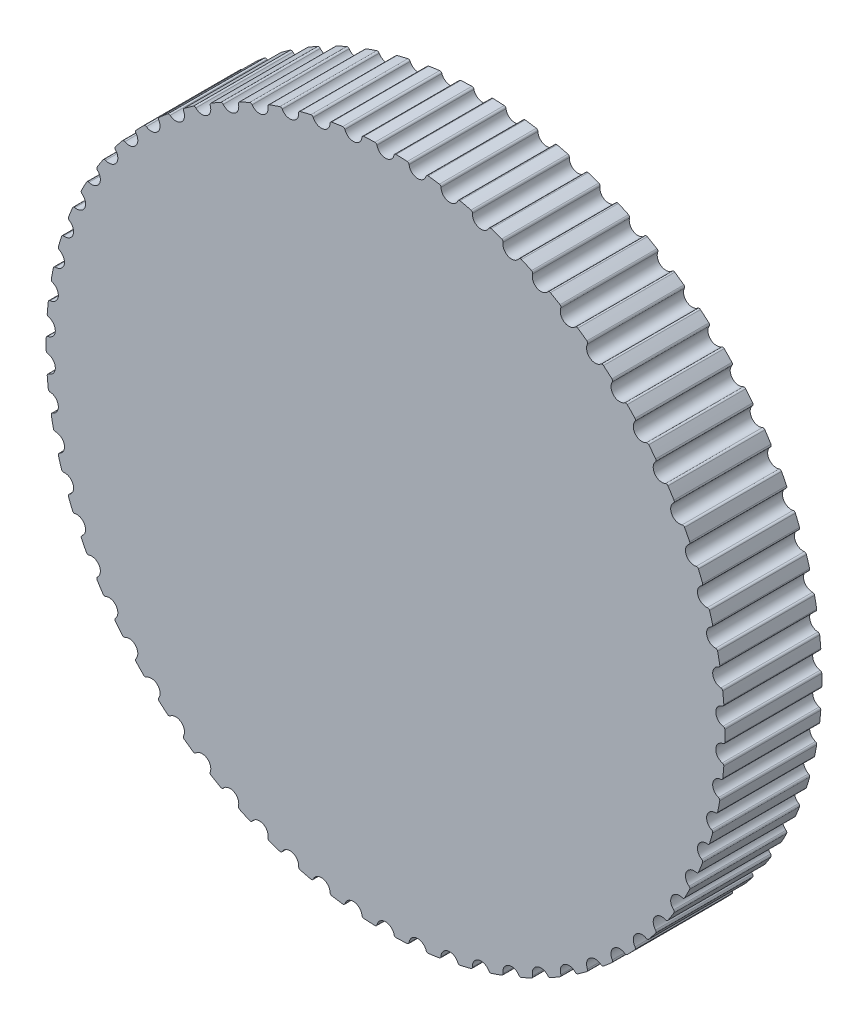
SolidWorks part; units mm, degrees
ref_plane "Front Plane" through (0, 0, 0) normal (0, 0, 1) x (1, 0, 0)
ref_plane "Top Plane" through (0, 0, 0) normal (0, 1, 0) x (1, 0, 0)
ref_plane "Right Plane" through (0, 0, 0) normal (1, 0, 0) x (0, 0, -1)
sketch "Sketch1" plane through (0, 0, 0) normal (0, 0, 1) x (1, 0, 0)
  arc A0 (-0.655, 20.9898) -> (0.655, 20.9898) centre (0, 0) ccw
  arc A1 (-0.5287, 20.8902) -> (0.5287, 20.8902) centre (0, 21) ccw
  arc A2 (0.5287, 20.8902) -> (0.655, 20.9898) centre (0.6511, 20.8648) cw
  arc A3 (-0.5287, 20.8902) -> (-0.655, 20.9898) centre (-0.6511, 20.8648) ccw
  arc A4 (1.3432, 20.957) -> (2.6473, 20.8325) centre (0, 0) ccw
  arc A5 (1.4594, 20.8459) -> (1.3432, 20.957) centre (1.3352, 20.8323) ccw
  arc A6 (1.4594, 20.8459) -> (2.5121, 20.7454) centre (1.9962, 20.9049) ccw
  arc A7 (2.5121, 20.7454) -> (2.6473, 20.8325) centre (2.6315, 20.7085) cw
  arc A8 (3.3292, 20.7344) -> (4.6155, 20.4865) centre (0, 0) ccw
  arc A9 (3.4343, 20.6128) -> (3.3292, 20.7344) centre (3.3093, 20.611) ccw
  arc A10 (3.4343, 20.6128) -> (4.4727, 20.4127) centre (3.9743, 20.6205) ccw
  arc A11 (4.4727, 20.4127) -> (4.6155, 20.4865) centre (4.5881, 20.3646) cw
  arc A12 (5.285, 20.3241) -> (6.542, 19.955) centre (0, 0) ccw
  arc A13 (5.3782, 20.193) -> (5.285, 20.3241) centre (5.2536, 20.2031) ccw
  arc A14 (5.3782, 20.193) -> (6.3928, 19.8951) centre (5.9164, 20.1494) ccw
  arc A15 (6.3928, 19.8951) -> (6.542, 19.955) centre (6.5031, 19.8362) cw
  arc A16 (7.193, 19.7297) -> (8.4092, 19.2428) centre (0, 0) ccw
  arc A17 (7.2733, 19.5903) -> (7.193, 19.7297) centre (7.1502, 19.6122) ccw
  arc A18 (7.2733, 19.5903) -> (8.255, 19.1973) centre (7.8049, 19.4957) ccw
  arc A19 (8.255, 19.1973) -> (8.4092, 19.2428) centre (8.3592, 19.1283) cw
  arc A20 (9.0359, 18.9566) -> (10.2003, 18.3563) centre (0, 0) ccw
  arc A21 (9.1025, 18.8103) -> (9.0359, 18.9566) centre (8.9821, 18.8438) ccw
  arc A22 (9.1025, 18.8103) -> (10.0424, 18.3257) centre (9.6228, 18.6655) ccw
  arc A23 (10.0424, 18.3257) -> (10.2003, 18.3563) centre (10.1396, 18.2471) cw
  arc A24 (10.7969, 18.0119) -> (11.899, 17.3036) centre (0, 0) ccw
  arc A25 (10.8493, 17.8598) -> (10.7969, 18.0119) centre (10.7326, 17.9046) ccw
  arc A26 (10.8493, 17.8598) -> (11.7389, 17.2881) centre (11.3535, 17.6663) ccw
  arc A27 (11.7389, 17.2881) -> (11.899, 17.3036) centre (11.8281, 17.2006) cw
  arc A28 (12.4601, 16.904) -> (13.4899, 16.0942) centre (0, 0) ccw
  arc A29 (12.4979, 16.7477) -> (12.4601, 16.904) centre (12.386, 16.8034) ccw
  arc A30 (12.4979, 16.7477) -> (13.3291, 16.094) centre (12.9813, 16.5071) ccw
  arc A31 (13.3291, 16.094) -> (13.4899, 16.0942) centre (13.4096, 15.9984) cw
  arc A32 (14.0105, 15.643) -> (14.9587, 14.739) centre (0, 0) ccw
  arc A33 (14.0333, 15.4838) -> (14.0105, 15.643) centre (13.9272, 15.5499) ccw
  arc A34 (14.0333, 15.4838) -> (14.7986, 14.7541) centre (14.4917, 15.1984) ccw
  arc A35 (14.7986, 14.7541) -> (14.9587, 14.739) centre (14.8696, 14.6513) cw
  arc A36 (15.4341, 14.2404) -> (16.292, 13.2504) centre (0, 0) ccw
  arc A37 (15.4416, 14.0798) -> (15.4341, 14.2404) centre (15.3422, 14.1557) ccw
  arc A38 (15.4416, 14.0798) -> (16.134, 13.2806) centre (15.8707, 13.7521) ccw
  arc A39 (16.134, 13.2806) -> (16.292, 13.2504) centre (16.195, 13.1715) cw
  arc A40 (16.7178, 12.7088) -> (17.4777, 11.6417) centre (0, 0) ccw
  arc A41 (16.71, 12.5482) -> (16.7178, 12.7088) centre (16.6183, 12.6332) ccw
  arc A42 (16.71, 12.5482) -> (17.3234, 11.6868) centre (17.1061, 12.1812) ccw
  arc A43 (17.3234, 11.6868) -> (17.4777, 11.6417) centre (17.3737, 11.5724) cw
  arc A44 (17.8502, 11.0622) -> (18.5052, 9.9276) centre (0, 0) ccw
  arc A45 (17.8271, 10.903) -> (17.8502, 11.0622) centre (17.7439, 10.9963) ccw
  arc A46 (17.8271, 10.903) -> (18.3559, 9.9872) centre (18.1865, 10.5) ccw
  arc A47 (18.3559, 9.9872) -> (18.5052, 9.9276) centre (18.395, 9.8685) cw
  arc A48 (18.8209, 9.3153) -> (19.3651, 8.1236) centre (0, 0) ccw
  arc A49 (18.7828, 9.1591) -> (18.8209, 9.3153) centre (18.7088, 9.2598) ccw
  arc A50 (18.7828, 9.1591) -> (19.2221, 8.1972) centre (19.1023, 8.7237) ccw
  arc A51 (19.2221, 8.1972) -> (19.3651, 8.1236) centre (19.2498, 8.0753) cw
  arc A52 (19.6211, 7.4841) -> (20.0496, 6.2461) centre (0, 0) ccw
  arc A53 (19.5684, 7.3322) -> (19.6211, 7.4841) centre (19.5043, 7.4395) ccw
  arc A54 (19.5684, 7.3322) -> (19.9142, 6.3329) centre (19.845, 6.8684) ccw
  arc A55 (19.9142, 6.3329) -> (20.0496, 6.2461) centre (19.9303, 6.2089) cw
  arc A56 (20.2437, 5.5851) -> (20.5525, 4.312) centre (0, 0) ccw
  arc A57 (20.1767, 5.4389) -> (20.2437, 5.5851) centre (20.1232, 5.5518) ccw
  arc A58 (20.1767, 5.4389) -> (20.426, 4.4112) centre (20.408, 4.9509) ccw
  arc A59 (20.426, 4.4112) -> (20.5525, 4.312) centre (20.4302, 4.2863) cw
  arc A60 (20.6829, 3.6355) -> (20.8694, 2.3388) centre (0, 0) ccw
  arc A61 (20.6024, 3.4963) -> (20.6829, 3.6355) centre (20.5598, 3.6139) ccw
  arc A62 (20.6024, 3.4963) -> (20.7529, 2.4496) centre (20.7863, 2.9886) ccw
  arc A63 (20.7529, 2.4496) -> (20.8694, 2.3388) centre (20.7451, 2.3249) cw
  arc A64 (20.9348, 1.653) -> (20.9972, 0.3445) centre (0, 0) ccw
  arc A65 (20.8414, 1.5221) -> (20.9348, 1.653) centre (20.8102, 1.6432) ccw
  arc A66 (20.8414, 1.5221) -> (20.8917, 0.4659) centre (20.9762, 0.9992) ccw
  arc A67 (20.8917, 0.4659) -> (20.9972, 0.3445) centre (20.8722, 0.3424) cw
  arc A68 (20.9972, -0.3445) -> (20.9348, -1.653) centre (0, 0) ccw
  arc A69 (20.8917, -0.4659) -> (20.9972, -0.3445) centre (20.8722, -0.3424) ccw
  arc A70 (20.8917, -0.4659) -> (20.8414, -1.5221) centre (20.9762, -0.9992) ccw
  arc A71 (20.8414, -1.5221) -> (20.9348, -1.653) centre (20.8102, -1.6432) cw
  arc A72 (20.8694, -2.3388) -> (20.6829, -3.6355) centre (0, 0) ccw
  arc A73 (20.7529, -2.4496) -> (20.8694, -2.3388) centre (20.7451, -2.3249) ccw
  arc A74 (20.7529, -2.4496) -> (20.6024, -3.4963) centre (20.7863, -2.9886) ccw
  arc A75 (20.6024, -3.4963) -> (20.6829, -3.6355) centre (20.5598, -3.6139) cw
  arc A76 (20.5525, -4.312) -> (20.2437, -5.5851) centre (0, 0) ccw
  arc A77 (20.426, -4.4112) -> (20.5525, -4.312) centre (20.4302, -4.2863) ccw
  arc A78 (20.426, -4.4112) -> (20.1767, -5.4389) centre (20.408, -4.9509) ccw
  arc A79 (20.1767, -5.4389) -> (20.2437, -5.5851) centre (20.1232, -5.5518) cw
  arc A80 (20.0496, -6.2461) -> (19.6211, -7.4841) centre (0, 0) ccw
  arc A81 (19.9142, -6.3329) -> (20.0496, -6.2461) centre (19.9303, -6.2089) ccw
  arc A82 (19.9142, -6.3329) -> (19.5684, -7.3322) centre (19.845, -6.8684) ccw
  arc A83 (19.5684, -7.3322) -> (19.6211, -7.4841) centre (19.5043, -7.4395) cw
  arc A84 (19.3651, -8.1236) -> (18.8209, -9.3153) centre (0, 0) ccw
  arc A85 (19.2221, -8.1972) -> (19.3651, -8.1236) centre (19.2498, -8.0753) ccw
  arc A86 (19.2221, -8.1972) -> (18.7828, -9.1591) centre (19.1023, -8.7237) ccw
  arc A87 (18.7828, -9.1591) -> (18.8209, -9.3153) centre (18.7088, -9.2598) cw
  arc A88 (18.5052, -9.9276) -> (17.8502, -11.0622) centre (0, 0) ccw
  arc A89 (18.3559, -9.9872) -> (18.5052, -9.9276) centre (18.395, -9.8685) ccw
  arc A90 (18.3559, -9.9872) -> (17.8271, -10.903) centre (18.1865, -10.5) ccw
  arc A91 (17.8271, -10.903) -> (17.8502, -11.0622) centre (17.7439, -10.9963) cw
  arc A92 (17.4777, -11.6417) -> (16.7178, -12.7088) centre (0, 0) ccw
  arc A93 (17.3234, -11.6868) -> (17.4777, -11.6417) centre (17.3737, -11.5724) ccw
  arc A94 (17.3234, -11.6868) -> (16.71, -12.5482) centre (17.1061, -12.1812) ccw
  arc A95 (16.71, -12.5482) -> (16.7178, -12.7088) centre (16.6183, -12.6332) cw
  arc A96 (16.292, -13.2504) -> (15.4341, -14.2404) centre (0, 0) ccw
  arc A97 (16.134, -13.2806) -> (16.292, -13.2504) centre (16.195, -13.1715) ccw
  arc A98 (16.134, -13.2806) -> (15.4416, -14.0798) centre (15.8707, -13.7521) ccw
  arc A99 (15.4416, -14.0798) -> (15.4341, -14.2404) centre (15.3422, -14.1557) cw
  arc A100 (14.9587, -14.739) -> (14.0105, -15.643) centre (0, 0) ccw
  arc A101 (14.7986, -14.7541) -> (14.9587, -14.739) centre (14.8696, -14.6513) ccw
  arc A102 (14.7986, -14.7541) -> (14.0333, -15.4838) centre (14.4917, -15.1984) ccw
  arc A103 (14.0333, -15.4838) -> (14.0105, -15.643) centre (13.9272, -15.5499) cw
  arc A104 (13.4899, -16.0942) -> (12.4601, -16.904) centre (0, 0) ccw
  arc A105 (13.3291, -16.094) -> (13.4899, -16.0942) centre (13.4096, -15.9984) ccw
  arc A106 (13.3291, -16.094) -> (12.4979, -16.7477) centre (12.9813, -16.5071) ccw
  arc A107 (12.4979, -16.7477) -> (12.4601, -16.904) centre (12.386, -16.8034) cw
  arc A108 (11.899, -17.3036) -> (10.7969, -18.0119) centre (0, 0) ccw
  arc A109 (11.7389, -17.2881) -> (11.899, -17.3036) centre (11.8281, -17.2006) ccw
  arc A110 (11.7389, -17.2881) -> (10.8493, -17.8598) centre (11.3535, -17.6663) ccw
  arc A111 (10.8493, -17.8598) -> (10.7969, -18.0119) centre (10.7326, -17.9046) cw
  arc A112 (10.2003, -18.3563) -> (9.0359, -18.9566) centre (0, 0) ccw
  arc A113 (10.0424, -18.3257) -> (10.2003, -18.3563) centre (10.1396, -18.2471) ccw
  arc A114 (10.0424, -18.3257) -> (9.1025, -18.8103) centre (9.6228, -18.6655) ccw
  arc A115 (9.1025, -18.8103) -> (9.0359, -18.9566) centre (8.9821, -18.8438) cw
  arc A116 (8.4092, -19.2428) -> (7.193, -19.7297) centre (0, 0) ccw
  arc A117 (8.255, -19.1973) -> (8.4092, -19.2428) centre (8.3592, -19.1283) ccw
  arc A118 (8.255, -19.1973) -> (7.2733, -19.5903) centre (7.8049, -19.4957) ccw
  arc A119 (7.2733, -19.5903) -> (7.193, -19.7297) centre (7.1502, -19.6122) cw
  arc A120 (6.542, -19.955) -> (5.285, -20.3241) centre (0, 0) ccw
  arc A121 (6.3928, -19.8951) -> (6.542, -19.955) centre (6.5031, -19.8362) ccw
  arc A122 (6.3928, -19.8951) -> (5.3782, -20.193) centre (5.9164, -20.1494) ccw
  arc A123 (5.3782, -20.193) -> (5.285, -20.3241) centre (5.2536, -20.2031) cw
  arc A124 (4.6155, -20.4865) -> (3.3292, -20.7344) centre (0, 0) ccw
  arc A125 (4.4727, -20.4127) -> (4.6155, -20.4865) centre (4.5881, -20.3646) ccw
  arc A126 (4.4727, -20.4127) -> (3.4343, -20.6128) centre (3.9743, -20.6205) ccw
  arc A127 (3.4343, -20.6128) -> (3.3292, -20.7344) centre (3.3093, -20.611) cw
  arc A128 (2.6473, -20.8325) -> (1.3432, -20.957) centre (0, 0) ccw
  arc A129 (2.5121, -20.7454) -> (2.6473, -20.8325) centre (2.6315, -20.7085) ccw
  arc A130 (2.5121, -20.7454) -> (1.4594, -20.8459) centre (1.9962, -20.9049) ccw
  arc A131 (1.4594, -20.8459) -> (1.3432, -20.957) centre (1.3352, -20.8323) cw
  arc A132 (0.655, -20.9898) -> (-0.655, -20.9898) centre (0, 0) ccw
  arc A133 (0.5287, -20.8902) -> (0.655, -20.9898) centre (0.6511, -20.8648) ccw
  arc A134 (0.5287, -20.8902) -> (-0.5287, -20.8902) centre (0, -21) ccw
  arc A135 (-0.5287, -20.8902) -> (-0.655, -20.9898) centre (-0.6511, -20.8648) cw
  arc A136 (-1.3432, -20.957) -> (-2.6473, -20.8325) centre (0, 0) ccw
  arc A137 (-1.4594, -20.8459) -> (-1.3432, -20.957) centre (-1.3352, -20.8323) ccw
  arc A138 (-1.4594, -20.8459) -> (-2.5121, -20.7454) centre (-1.9962, -20.9049) ccw
  arc A139 (-2.5121, -20.7454) -> (-2.6473, -20.8325) centre (-2.6315, -20.7085) cw
  arc A140 (-3.3292, -20.7344) -> (-4.6155, -20.4865) centre (0, 0) ccw
  arc A141 (-3.4343, -20.6128) -> (-3.3292, -20.7344) centre (-3.3093, -20.611) ccw
  arc A142 (-3.4343, -20.6128) -> (-4.4727, -20.4127) centre (-3.9743, -20.6205) ccw
  arc A143 (-4.4727, -20.4127) -> (-4.6155, -20.4865) centre (-4.5881, -20.3646) cw
  arc A144 (-5.285, -20.3241) -> (-6.542, -19.955) centre (0, 0) ccw
  arc A145 (-5.3782, -20.193) -> (-5.285, -20.3241) centre (-5.2536, -20.2031) ccw
  arc A146 (-5.3782, -20.193) -> (-6.3928, -19.8951) centre (-5.9164, -20.1494) ccw
  arc A147 (-6.3928, -19.8951) -> (-6.542, -19.955) centre (-6.5031, -19.8362) cw
  arc A148 (-7.193, -19.7297) -> (-8.4092, -19.2428) centre (0, 0) ccw
  arc A149 (-7.2733, -19.5903) -> (-7.193, -19.7297) centre (-7.1502, -19.6122) ccw
  arc A150 (-7.2733, -19.5903) -> (-8.255, -19.1973) centre (-7.8049, -19.4957) ccw
  arc A151 (-8.255, -19.1973) -> (-8.4092, -19.2428) centre (-8.3592, -19.1283) cw
  arc A152 (-9.0359, -18.9566) -> (-10.2003, -18.3563) centre (0, 0) ccw
  arc A153 (-9.1025, -18.8103) -> (-9.0359, -18.9566) centre (-8.9821, -18.8438) ccw
  arc A154 (-9.1025, -18.8103) -> (-10.0424, -18.3257) centre (-9.6228, -18.6655) ccw
  arc A155 (-10.0424, -18.3257) -> (-10.2003, -18.3563) centre (-10.1396, -18.2471) cw
  arc A156 (-10.7969, -18.0119) -> (-11.899, -17.3036) centre (0, 0) ccw
  arc A157 (-10.8493, -17.8598) -> (-10.7969, -18.0119) centre (-10.7326, -17.9046) ccw
  arc A158 (-10.8493, -17.8598) -> (-11.7389, -17.2881) centre (-11.3535, -17.6663) ccw
  arc A159 (-11.7389, -17.2881) -> (-11.899, -17.3036) centre (-11.8281, -17.2006) cw
  arc A160 (-12.4601, -16.904) -> (-13.4899, -16.0942) centre (0, 0) ccw
  arc A161 (-12.4979, -16.7477) -> (-12.4601, -16.904) centre (-12.386, -16.8034) ccw
  arc A162 (-12.4979, -16.7477) -> (-13.3291, -16.094) centre (-12.9813, -16.5071) ccw
  arc A163 (-13.3291, -16.094) -> (-13.4899, -16.0942) centre (-13.4096, -15.9984) cw
  arc A164 (-14.0105, -15.643) -> (-14.9587, -14.739) centre (0, 0) ccw
  arc A165 (-14.0333, -15.4838) -> (-14.0105, -15.643) centre (-13.9272, -15.5499) ccw
  arc A166 (-14.0333, -15.4838) -> (-14.7986, -14.7541) centre (-14.4917, -15.1984) ccw
  arc A167 (-14.7986, -14.7541) -> (-14.9587, -14.739) centre (-14.8696, -14.6513) cw
  arc A168 (-15.4341, -14.2404) -> (-16.292, -13.2504) centre (0, 0) ccw
  arc A169 (-15.4416, -14.0798) -> (-15.4341, -14.2404) centre (-15.3422, -14.1557) ccw
  arc A170 (-15.4416, -14.0798) -> (-16.134, -13.2806) centre (-15.8707, -13.7521) ccw
  arc A171 (-16.134, -13.2806) -> (-16.292, -13.2504) centre (-16.195, -13.1715) cw
  arc A172 (-16.7178, -12.7088) -> (-17.4777, -11.6417) centre (0, 0) ccw
  arc A173 (-16.71, -12.5482) -> (-16.7178, -12.7088) centre (-16.6183, -12.6332) ccw
  arc A174 (-16.71, -12.5482) -> (-17.3234, -11.6868) centre (-17.1061, -12.1812) ccw
  arc A175 (-17.3234, -11.6868) -> (-17.4777, -11.6417) centre (-17.3737, -11.5724) cw
  arc A176 (-17.8502, -11.0622) -> (-18.5052, -9.9276) centre (0, 0) ccw
  arc A177 (-17.8271, -10.903) -> (-17.8502, -11.0622) centre (-17.7439, -10.9963) ccw
  arc A178 (-17.8271, -10.903) -> (-18.3559, -9.9872) centre (-18.1865, -10.5) ccw
  arc A179 (-18.3559, -9.9872) -> (-18.5052, -9.9276) centre (-18.395, -9.8685) cw
  arc A180 (-18.8209, -9.3153) -> (-19.3651, -8.1236) centre (0, 0) ccw
  arc A181 (-18.7828, -9.1591) -> (-18.8209, -9.3153) centre (-18.7088, -9.2598) ccw
  arc A182 (-18.7828, -9.1591) -> (-19.2221, -8.1972) centre (-19.1023, -8.7237) ccw
  arc A183 (-19.2221, -8.1972) -> (-19.3651, -8.1236) centre (-19.2498, -8.0753) cw
  arc A184 (-19.6211, -7.4841) -> (-20.0496, -6.2461) centre (0, 0) ccw
  arc A185 (-19.5684, -7.3322) -> (-19.6211, -7.4841) centre (-19.5043, -7.4395) ccw
  arc A186 (-19.5684, -7.3322) -> (-19.9142, -6.3329) centre (-19.845, -6.8684) ccw
  arc A187 (-19.9142, -6.3329) -> (-20.0496, -6.2461) centre (-19.9303, -6.2089) cw
  arc A188 (-20.2437, -5.5851) -> (-20.5525, -4.312) centre (0, 0) ccw
  arc A189 (-20.1767, -5.4389) -> (-20.2437, -5.5851) centre (-20.1232, -5.5518) ccw
  arc A190 (-20.1767, -5.4389) -> (-20.426, -4.4112) centre (-20.408, -4.9509) ccw
  arc A191 (-20.426, -4.4112) -> (-20.5525, -4.312) centre (-20.4302, -4.2863) cw
  arc A192 (-20.6829, -3.6355) -> (-20.8694, -2.3388) centre (0, 0) ccw
  arc A193 (-20.6024, -3.4963) -> (-20.6829, -3.6355) centre (-20.5598, -3.6139) ccw
  arc A194 (-20.6024, -3.4963) -> (-20.7529, -2.4496) centre (-20.7863, -2.9886) ccw
  arc A195 (-20.7529, -2.4496) -> (-20.8694, -2.3388) centre (-20.7451, -2.3249) cw
  arc A196 (-20.9348, -1.653) -> (-20.9972, -0.3445) centre (0, 0) ccw
  arc A197 (-20.8414, -1.5221) -> (-20.9348, -1.653) centre (-20.8102, -1.6432) ccw
  arc A198 (-20.8414, -1.5221) -> (-20.8917, -0.4659) centre (-20.9762, -0.9992) ccw
  arc A199 (-20.8917, -0.4659) -> (-20.9972, -0.3445) centre (-20.8722, -0.3424) cw
  arc A200 (-20.9972, 0.3445) -> (-20.9348, 1.653) centre (0, 0) ccw
  arc A201 (-20.8917, 0.4659) -> (-20.9972, 0.3445) centre (-20.8722, 0.3424) ccw
  arc A202 (-20.8917, 0.4659) -> (-20.8414, 1.5221) centre (-20.9762, 0.9992) ccw
  arc A203 (-20.8414, 1.5221) -> (-20.9348, 1.653) centre (-20.8102, 1.6432) cw
  arc A204 (-20.8694, 2.3388) -> (-20.6829, 3.6355) centre (0, 0) ccw
  arc A205 (-20.7529, 2.4496) -> (-20.8694, 2.3388) centre (-20.7451, 2.3249) ccw
  arc A206 (-20.7529, 2.4496) -> (-20.6024, 3.4963) centre (-20.7863, 2.9886) ccw
  arc A207 (-20.6024, 3.4963) -> (-20.6829, 3.6355) centre (-20.5598, 3.6139) cw
  arc A208 (-20.5525, 4.312) -> (-20.2437, 5.5851) centre (0, 0) ccw
  arc A209 (-20.426, 4.4112) -> (-20.5525, 4.312) centre (-20.4302, 4.2863) ccw
  arc A210 (-20.426, 4.4112) -> (-20.1767, 5.4389) centre (-20.408, 4.9509) ccw
  arc A211 (-20.1767, 5.4389) -> (-20.2437, 5.5851) centre (-20.1232, 5.5518) cw
  arc A212 (-20.0496, 6.2461) -> (-19.6211, 7.4841) centre (0, 0) ccw
  arc A213 (-19.9142, 6.3329) -> (-20.0496, 6.2461) centre (-19.9303, 6.2089) ccw
  arc A214 (-19.9142, 6.3329) -> (-19.5684, 7.3322) centre (-19.845, 6.8684) ccw
  arc A215 (-19.5684, 7.3322) -> (-19.6211, 7.4841) centre (-19.5043, 7.4395) cw
  arc A216 (-19.3651, 8.1236) -> (-18.8209, 9.3153) centre (0, 0) ccw
  arc A217 (-19.2221, 8.1972) -> (-19.3651, 8.1236) centre (-19.2498, 8.0753) ccw
  arc A218 (-19.2221, 8.1972) -> (-18.7828, 9.1591) centre (-19.1023, 8.7237) ccw
  arc A219 (-18.7828, 9.1591) -> (-18.8209, 9.3153) centre (-18.7088, 9.2598) cw
  arc A220 (-18.5052, 9.9276) -> (-17.8502, 11.0622) centre (0, 0) ccw
  arc A221 (-18.3559, 9.9872) -> (-18.5052, 9.9276) centre (-18.395, 9.8685) ccw
  arc A222 (-18.3559, 9.9872) -> (-17.8271, 10.903) centre (-18.1865, 10.5) ccw
  arc A223 (-17.8271, 10.903) -> (-17.8502, 11.0622) centre (-17.7439, 10.9963) cw
  arc A224 (-17.4777, 11.6417) -> (-16.7178, 12.7088) centre (0, 0) ccw
  arc A225 (-17.3234, 11.6868) -> (-17.4777, 11.6417) centre (-17.3737, 11.5724) ccw
  arc A226 (-17.3234, 11.6868) -> (-16.71, 12.5482) centre (-17.1061, 12.1812) ccw
  arc A227 (-16.71, 12.5482) -> (-16.7178, 12.7088) centre (-16.6183, 12.6332) cw
  arc A228 (-16.292, 13.2504) -> (-15.4341, 14.2404) centre (0, 0) ccw
  arc A229 (-16.134, 13.2806) -> (-16.292, 13.2504) centre (-16.195, 13.1715) ccw
  arc A230 (-16.134, 13.2806) -> (-15.4416, 14.0798) centre (-15.8707, 13.7521) ccw
  arc A231 (-15.4416, 14.0798) -> (-15.4341, 14.2404) centre (-15.3422, 14.1557) cw
  arc A232 (-14.9587, 14.739) -> (-14.0105, 15.643) centre (0, 0) ccw
  arc A233 (-14.7986, 14.7541) -> (-14.9587, 14.739) centre (-14.8696, 14.6513) ccw
  arc A234 (-14.7986, 14.7541) -> (-14.0333, 15.4838) centre (-14.4917, 15.1984) ccw
  arc A235 (-14.0333, 15.4838) -> (-14.0105, 15.643) centre (-13.9272, 15.5499) cw
  arc A236 (-13.4899, 16.0942) -> (-12.4601, 16.904) centre (0, 0) ccw
  arc A237 (-13.3291, 16.094) -> (-13.4899, 16.0942) centre (-13.4096, 15.9984) ccw
  arc A238 (-13.3291, 16.094) -> (-12.4979, 16.7477) centre (-12.9813, 16.5071) ccw
  arc A239 (-12.4979, 16.7477) -> (-12.4601, 16.904) centre (-12.386, 16.8034) cw
  arc A240 (-11.899, 17.3036) -> (-10.7969, 18.0119) centre (0, 0) ccw
  arc A241 (-11.7389, 17.2881) -> (-11.899, 17.3036) centre (-11.8281, 17.2006) ccw
  arc A242 (-11.7389, 17.2881) -> (-10.8493, 17.8598) centre (-11.3535, 17.6663) ccw
  arc A243 (-10.8493, 17.8598) -> (-10.7969, 18.0119) centre (-10.7326, 17.9046) cw
  arc A244 (-10.2003, 18.3563) -> (-9.0359, 18.9566) centre (0, 0) ccw
  arc A245 (-10.0424, 18.3257) -> (-10.2003, 18.3563) centre (-10.1396, 18.2471) ccw
  arc A246 (-10.0424, 18.3257) -> (-9.1025, 18.8103) centre (-9.6228, 18.6655) ccw
  arc A247 (-9.1025, 18.8103) -> (-9.0359, 18.9566) centre (-8.9821, 18.8438) cw
  arc A248 (-8.4092, 19.2428) -> (-7.193, 19.7297) centre (0, 0) ccw
  arc A249 (-8.255, 19.1973) -> (-8.4092, 19.2428) centre (-8.3592, 19.1283) ccw
  arc A250 (-8.255, 19.1973) -> (-7.2733, 19.5903) centre (-7.8049, 19.4957) ccw
  arc A251 (-7.2733, 19.5903) -> (-7.193, 19.7297) centre (-7.1502, 19.6122) cw
  arc A252 (-6.542, 19.955) -> (-5.285, 20.3241) centre (0, 0) ccw
  arc A253 (-6.3928, 19.8951) -> (-6.542, 19.955) centre (-6.5031, 19.8362) ccw
  arc A254 (-6.3928, 19.8951) -> (-5.3782, 20.193) centre (-5.9164, 20.1494) ccw
  arc A255 (-5.3782, 20.193) -> (-5.285, 20.3241) centre (-5.2536, 20.2031) cw
  arc A256 (-4.6155, 20.4865) -> (-3.3292, 20.7344) centre (0, 0) ccw
  arc A257 (-4.4727, 20.4127) -> (-4.6155, 20.4865) centre (-4.5881, 20.3646) ccw
  arc A258 (-4.4727, 20.4127) -> (-3.4343, 20.6128) centre (-3.9743, 20.6205) ccw
  arc A259 (-3.4343, 20.6128) -> (-3.3292, 20.7344) centre (-3.3093, 20.611) cw
  arc A260 (-2.6473, 20.8325) -> (-1.3432, 20.957) centre (0, 0) ccw
  arc A261 (-2.5121, 20.7454) -> (-2.6473, 20.8325) centre (-2.6315, 20.7085) ccw
  arc A262 (-2.5121, 20.7454) -> (-1.4594, 20.8459) centre (-1.9962, 20.9049) ccw
  arc A263 (-1.4594, 20.8459) -> (-1.3432, 20.957) centre (-1.3352, 20.8323) cw
  point P467 (0, 0)
  dimension "D1" = 0.125
  dimension "D2" = 66
extrude "Boss-Extrude1" add sketch "Sketch1" along normal blind 6 contours A263 A262 A261 A0 A259 A258 A257 A255 A254 A253 A251 A250 A249 A247 A246 A245 A243 A242 A241 A239 A238 A237 A235 A234 A233 A231 A230 A229 A227 A226 A225 A223 A222 A221 A219 A218 A217 A215 A214 A213
